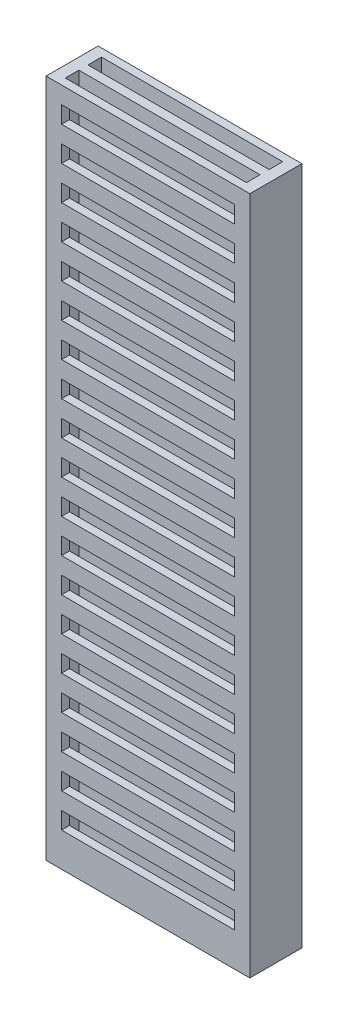
SolidWorks part; units mm, degrees
ref_plane "Front Plane" through (0, 0, 0) normal (0, 0, 1) x (1, 0, 0)
ref_plane "Top Plane" through (0, 0, 0) normal (0, 1, 0) x (1, 0, 0)
ref_plane "Right Plane" through (0, 0, 0) normal (1, 0, 0) x (0, 0, -1)
sketch "Sketch1" plane through (0, 0, 0) normal (0, 1, 0) x (1, 0, 0)
  line L1 (-4.5, -1.15) -> (4.5, -1.15)
  line L2 (-4.5, -1.15) -> (-4.5, 1.15)
  line L3 (-4.5, 1.15) -> (4.5, 1.15)
  line L4 (4.5, -1.15) -> (4.5, 1.15)
  line L5 (-4.5, -1.15) -> (4.5, 1.15) construction
  line L6 (-4.5, 1.15) -> (4.5, -1.15) construction
  point P0 (0, 0)
  dimension "D1" = 9
  dimension "D2" = 2.3
extrude "Boss-Extrude1" add sketch "Sketch1" along normal mid plane 30
sketch "Sketch2" plane through (0, 15, 0) normal (0, 1, 0) x (1, 0, 0)
  line L1 (-4, 0.2) -> (4, 0.2)
  line L2 (-4, 0.2) -> (-4, 0.8)
  line L3 (-4, 0.8) -> (4, 0.8)
  line L4 (4, 0.2) -> (4, 0.8)
  line L5 (-4, 0.2) -> (4, 0.8) construction
  line L6 (-4, 0.8) -> (4, 0.2) construction
  point P0 (0, 0.5)
  dimension "D1" = 0.6
  dimension "D2" = 8
  dimension "D3" = 0
  dimension "D4" = 0.5
extrude "Cut-Extrude1" cut sketch "Sketch2" against normal through all and the other way through all
mirror "Mirror1" about plane through (0, 0, 0) normal (0, 0, 1) of "Cut-Extrude1"
sketch "Sketch3" plane through (0, 0, 1.15) normal (0, 0, 1) x (1, 0, 0)
  line L0 (0, -1.65) -> (0, 1.65) construction
  line L1 (-3.8171, 13.5) -> (3.8171, 13.5)
  line L2 (-3.8171, 13.5) -> (-3.8171, 14.25)
  line L3 (-3.8171, 14.25) -> (3.8171, 14.25)
  line L4 (3.8171, 13.5) -> (3.8171, 14.25)
  line L5 (-3.8171, 13.5) -> (3.8171, 14.25) construction
  line L6 (-3.8171, 14.25) -> (3.8171, 13.5) construction
  line L7 (-4.5, 15) -> (4.5, 15) construction
  point P0 (0, 13.875)
  dimension "D1" = 0.75
  dimension "D2" = 0.75
extrude "Cut-Extrude2" cut sketch "Sketch3" against normal up to next (0.35 mm away)
pattern_linear "LPattern1" count 19 spacing 1.5 along (0, -1, 0) of "Cut-Extrude2"
mirror "Mirror2" about plane through (0, 0, 0) normal (0, 0, 1) of "LPattern1", "Cut-Extrude2"
